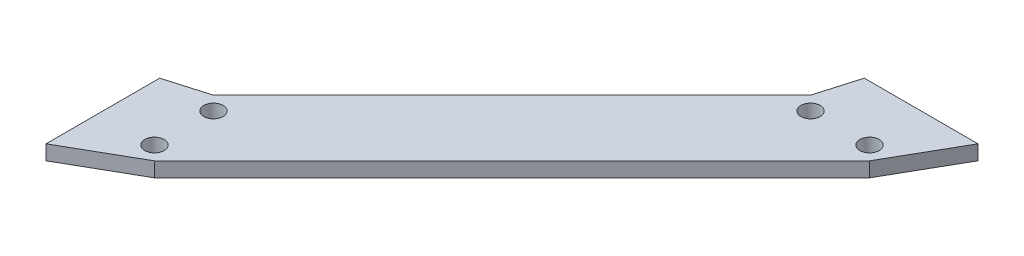
SolidWorks part; units mm, degrees
ref_plane "Front Plane" through (0, 0, 0) normal (0, 0, 1) x (1, 0, 0)
ref_plane "Top Plane" through (0, 0, 0) normal (0, 1, 0) x (1, 0, 0)
ref_plane "Right Plane" through (0, 0, 0) normal (1, 0, 0) x (0, 0, -1)
sketch "Sketch1" plane through (0, 0, 0) normal (0, 1, 0) x (1, 0, 0)
  line L0 (0, 0) -> (82.7873, -82.7873) construction
  line L1 (0, 0) -> (0, -11.9062) construction
  line L2 (0, -11.9062) -> (76.2, -11.9062) construction
  line L3 (76.2, -11.9062) -> (88.9, -11.9062) construction
  line L4 (76.2, 0) -> (88.9, 0)
  line L5 (74.1172, -11.9062) -> (70.9422, -11.9062) construction
  line L6 (76.2, -11.9062) -> (73.2545, -8.9607) construction
  line L7 (73.2545, -8.9607) -> (75.8652, 0)
  line L8 (75.8652, 0) -> (76.2, 0)
  line L9 (73.2545, -8.9607) -> (8.9607, -73.2545)
  line L10 (88.9, -11.9062) -> (91.8455, -14.8518) construction
  line L11 (91.8455, -14.8518) -> (100.3473, 0)
  line L12 (100.3473, 0) -> (88.9, 0)
  line L13 (91.8455, -14.8518) -> (14.8518, -91.8455)
  line L14 (14.8518, -91.8455) -> (0, -100.3473)
  line L15 (0, -100.3473) -> (0, -88.9)
  line L16 (0, -76.2) -> (0, -88.9)
  line L17 (0, -75.8652) -> (0, -76.2)
  line L18 (8.9607, -73.2545) -> (0, -75.8652)
  circle A0 centre (76.2, -11.9062) radius 2.0828
  circle A1 centre (88.9, -11.9062) radius 2.0828
  circle A2 centre (11.9062, -76.2) radius 2.0828
  circle A3 centre (11.9062, -88.9) radius 2.0828
  point P12 (0, 0)
  point P24 (53.3486, -53.3486)
  point P28 (41.1076, -41.1076)
  dimension "D3" = 12.7
  dimension "D1" = 76.2
  dimension "D2" = 45
  dimension "D4" = 11.9062
  dimension "D5" = 4.1656
  dimension "D6" = 45
  dimension "D7" = 4.1656
  dimension "D8" = 135
extrude "Boss-Extrude1" add sketch "Sketch1" along normal blind 3.175
